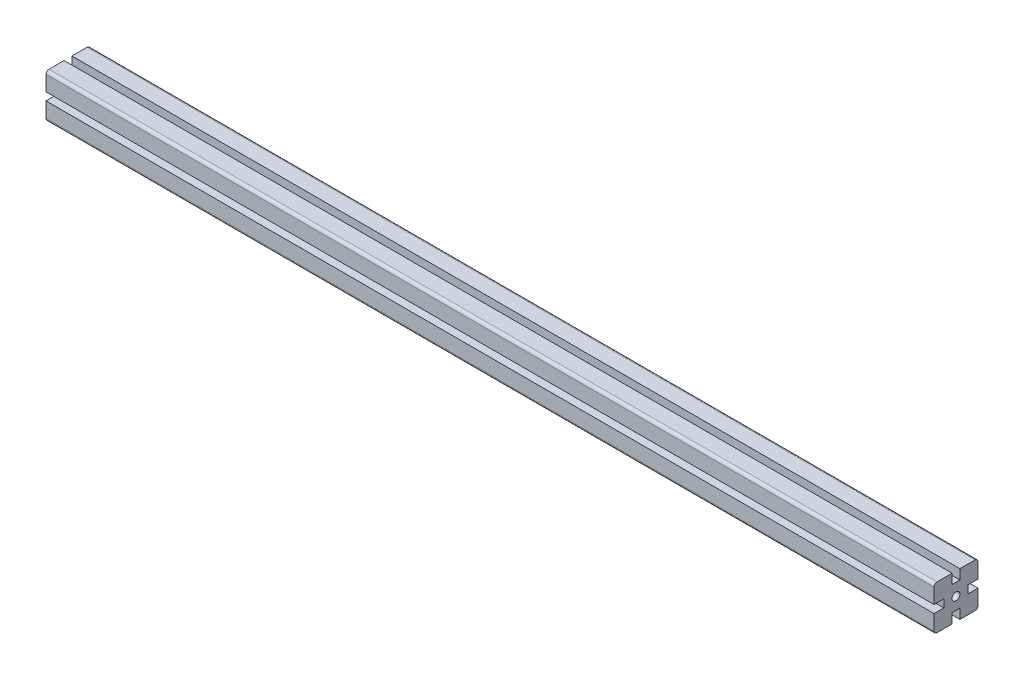
SolidWorks part; units mm, degrees
ref_plane "Plan de face" through (0, 0, 0) normal (0, 0, 1) x (1, 0, 0)
ref_plane "Plan de dessus" through (0, 0, 0) normal (0, 1, 0) x (1, 0, 0)
ref_plane "Plan de droite" through (0, 0, 0) normal (1, 0, 0) x (0, 0, -1)
ref_plane "Plan1" through (1000, 0, 0) normal (1, 0, 0) x (0, 0, -1)
sketch "Esquisse1" plane through (1000, 0, 0) normal (1, 0, 0) x (0, 0, -1)
  line L20 (22.5, -4) -> (12.5, -4)
  line L21 (12.5, -4) -> (12.5, 4)
  line L22 (12.5, 4) -> (22.5, 4)
  line L23 (22.5, 4) -> (22.5, 22.5)
  line L24 (22.5, 22.5) -> (4, 22.5)
  line L25 (4, 22.5) -> (4, 12.5)
  line L26 (4, 12.5) -> (-4, 12.5)
  line L27 (-4, 12.5) -> (-4, 22.5)
  line L28 (-4, 22.5) -> (-22.5, 22.5)
  line L29 (-22.5, 22.5) -> (-22.5, 4)
  line L30 (-22.5, 4) -> (-12.5, 4)
  line L31 (-12.5, 4) -> (-12.5, -4)
  line L32 (-12.5, -4) -> (-22.5, -4)
  line L33 (-22.5, -4) -> (-22.5, -22.5)
  line L34 (-22.5, -22.5) -> (-4, -22.5)
  line L35 (-4, -22.5) -> (-4, -12.5)
  line L36 (-4, -12.5) -> (4, -12.5)
  line L37 (4, -12.5) -> (4, -22.5)
  line L38 (4, -22.5) -> (22.5, -22.5)
  line L39 (22.5, -22.5) -> (22.5, -4)
  line L40 (0, 0) -> (22.5, 0) construction
  line L41 (0, 0) -> (0, 22.5) construction
  circle A1 centre (0, 0) radius 4
  dimension "D1" = 4
  dimension "D2" = 45
  dimension "D3" = 45
  dimension "D4" = 4
  dimension "D5" = 10
  dimension "D6" = 10
  dimension "D7" = 10
  dimension "D8" = 10
  dimension "D9" = 22.5
extrude "Boss.-Extru.1" add sketch "Esquisse1" against normal blind 908
fillet "Fillet1" radius 3 4 edges at (546, -22.5, 22.5) (546, -22.5, -22.5) (546, 22.5, 22.5) (546, 22.5, -22.5)
